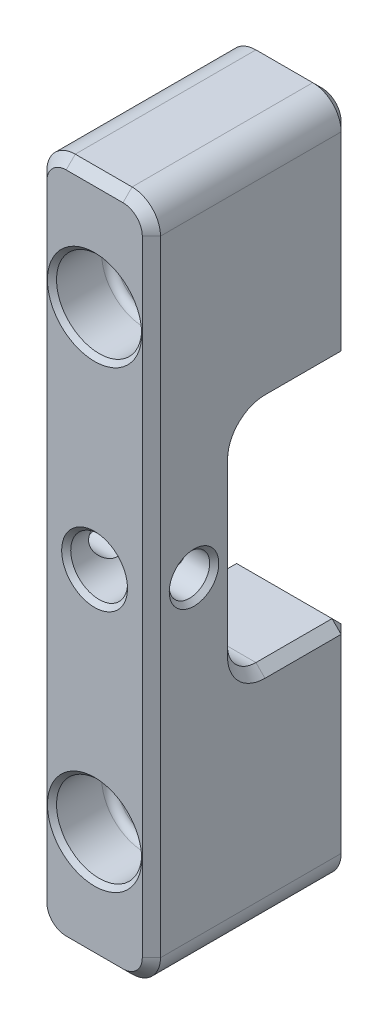
SolidWorks part; units mm, degrees
ref_plane "Front Plane" through (0, 0, 0) normal (0, 0, 1) x (1, 0, 0)
ref_plane "Top Plane" through (0, 0, 0) normal (0, 1, 0) x (1, 0, 0)
ref_plane "Right Plane" through (0, 0, 0) normal (1, 0, 0) x (0, 0, -1)
sketch "Sketch1" plane through (0, 0, 0) normal (0, 0, 1) x (1, 0, 0)
  line L1 (-3.175, -19.05) -> (3.175, -19.05)
  line L2 (-3.175, -19.05) -> (-3.175, 19.05)
  line L3 (-3.175, 19.05) -> (3.175, 19.05)
  line L4 (3.175, -19.05) -> (3.175, 19.05)
  line L5 (-3.175, -19.05) -> (3.175, 19.05) construction
  line L6 (-3.175, 19.05) -> (3.175, -19.05) construction
  point P0 (0, 0)
  dimension "D1" = 6.35
  dimension "D2" = 38.1
extrude "Boss-Extrude1" add sketch "Sketch1" along normal mid plane 11.1125 contours L3 L4 L1 L2
sketch "Sketch8" plane through (0, 0, 0) normal (1, 0, 0) x (0, 0, -1)
  line L0 (5.5562, -19.05) -> (5.5562, 19.05) construction
  line L1 (-0.7937, 6.35) -> (5.5562, 6.35)
  line L2 (-0.7937, 6.35) -> (-0.7937, -6.35)
  line L3 (-0.7937, -6.35) -> (5.5562, -6.35)
  line L4 (5.5562, 6.35) -> (5.5562, -6.35)
  line L5 (-5.5562, 19.05) -> (5.5562, 19.05) construction
  point P6 (-0.7937, 0)
  dimension "D1" = 6.35
  dimension "D2" = 12.7
extrude "Cut-Extrude1" cut sketch "Sketch8" against normal through all both and the other way through all contours L1 L4 L3 L2
hole_wizard "1/8 (0.125) Diameter Hole1" positions "Sketch2" profile "Sketch3" hole size "1/8" standard "ANSI Inch" end condition through all
sketch "Sketch2" plane through (0, 0, 5.5562) normal (0, 0, 1) x (1, 0, 0)
  point P0 (0, 0)
sketch "Sketch3" plane through (0, 0, 5.5562) normal (1, 0, 0) x (0, -1, 0)
  line L0 (0, 0) -> (0, 11.1125)
  line L1 (0, 11.1125) -> (1.5875, 11.1125)
  line L2 (1.5875, 11.1125) -> (1.5875, 0)
  line L5 (1.5875, 0) -> (0, 0)
  line L11 (0, -6.35) -> (0, 107.95) construction
  dimension "Thru Hole Dia." = 3.175
  dimension "Thru Hole Depth" = 11.1125
hole_wizard "CBORE for #2 Binding Head Machine Screw2" positions "Sketch4" profile "Sketch5" counterbore size "#2" standard "ANSI Inch" end condition through all
sketch "Sketch4" plane through (0, 0, 5.5562) normal (0, 0, 1) x (1, 0, 0)
  line L0 (-3.175, 19.05) -> (3.175, 19.05) construction
  line L1 (-3.175, -19.05) -> (3.175, -19.05) construction
  point P0 (0, 12.7)
  point P2 (0, -12.7)
  dimension "D1" = 6.35
  dimension "D2" = 6.35
sketch "Sketch5" plane through (0, 12.7, 5.5562) normal (1, 0, 0) x (0, -1, 0)
  line L0 (0, 0) -> (0, 11.1125)
  line L1 (0, 11.1125) -> (1.2192, 11.1125)
  line L3 (1.2192, 11.1125) -> (1.2192, 3.175)
  line L4 (1.2192, 3.175) -> (2.3812, 3.175)
  line L5 (2.3812, 3.175) -> (2.3812, 0)
  line L7 (2.3812, 0) -> (0, 0)
  line L11 (0, -6.35) -> (0, 107.95) construction
  dimension "Thru Hole Dia." = 2.4384
  dimension "Thru Hole Depth" = 11.1125
  dimension "C'Bore Dia." = 4.7625
  dimension "C'Bore Depth" = 3.175
hole_wizard "#4-40 Tapped Hole1" positions "Sketch6" profile "Sketch7" tap size "#4-40" standard "ANSI Inch" end condition through all
sketch "Sketch6" plane through (3.175, 0, 0) normal (1, 0, 0) x (0, 0, -1)
  line L0 (-0.7937, 0) -> (-5.5562, 0) construction
  line L1 (-0.7937, 6.35) -> (-0.7937, -6.35) construction
  line L2 (-5.5562, -19.05) -> (-5.5562, 19.05) construction
  point P0 (-3.175, 0)
sketch "Sketch7" plane through (3.175, 0, 3.175) normal (0, 1, 0) x (0, 0, -1)
  line L0 (0, 0) -> (0, 6.35)
  line L1 (0, 6.35) -> (1.1303, 6.35)
  line L2 (1.1303, 6.35) -> (1.1303, 0)
  line L5 (1.1303, 0) -> (0, 0)
  line L11 (0, -6.35) -> (0, 107.95) construction
  dimension "Thru Tap Drill Dia." = 2.2606
  dimension "Thru Tap Drill Depth" = 6.35
cosmetic thread "Hole Thread1" parameters "D2"=2.8448
fillet "Fillet1" radius 1.5875 6 edges at (-3.175, -19.05, 0) (3.175, -19.05, 0) (-3.175, 19.05, 0) (3.175, 19.05, 0) (0, -6.35, 0.7937) (0, 6.35, 0.7937)
fillet "Fillet2" radius 0.3969 2 edges at (2.3812, -12.7, 2.3812) (2.3812, 12.7, 2.3812)
chamfer "Chamfer1" distance 0.508 angle 45 30 edges at (-3.175, -11.9063, -5.5562) (-3.175, 11.9062, -5.5562) (-2.71, -18.585, -5.5562) (-2.71, 18.585, -5.5562) (0, -19.05, -5.5562) (0, 19.05, -5.5562) (2.71, -18.585, -5.5562) (2.71, 18.585, -5.5562) (3.175, -11.9063, -5.5562) (3.175, 11.9062, -5.5562) (-3.175, 0, 5.5562) (-2.71, -18.585, 5.5562) (-2.71, 18.585, 5.5562) (0, -19.05, 5.5562) (0, 19.05, 5.5562) (2.71, -18.585, 5.5562) (2.71, 18.585, 5.5562) (3.175, 0, 5.5562) (-3.175, -6.35, -3.175) (3.175, -6.35, -3.175) (-3.175, -5.885, 0.3288) (3.175, -5.885, 0.3288) (-3.175, 0, 0.7937) (3.175, 0, 0.7937) (-3.175, 5.885, 0.3288) (3.175, 5.885, 0.3288) (-3.175, 6.35, -3.175) (3.175, 6.35, -3.175) (0, 6.35, -5.5562) (0, -6.35, -5.5562)
chamfer "Chamfer2" distance 0.254 angle 45 10 edges at (-3.175, 0, 2.0447) (3.175, 0, 2.0447) (1.2192, -12.7, -5.5562) (1.5875, 0, 0.7937) (1.2192, 12.7, -5.5562) (1.2192, -12.7, 2.3812) (2.3812, -12.7, 5.5562) (1.5875, 0, 5.5563) (1.2192, 12.7, 2.3812) (2.3812, 12.7, 5.5562)
equation "\"D2@Sketch4\"=\"D1@Sketch4\""
